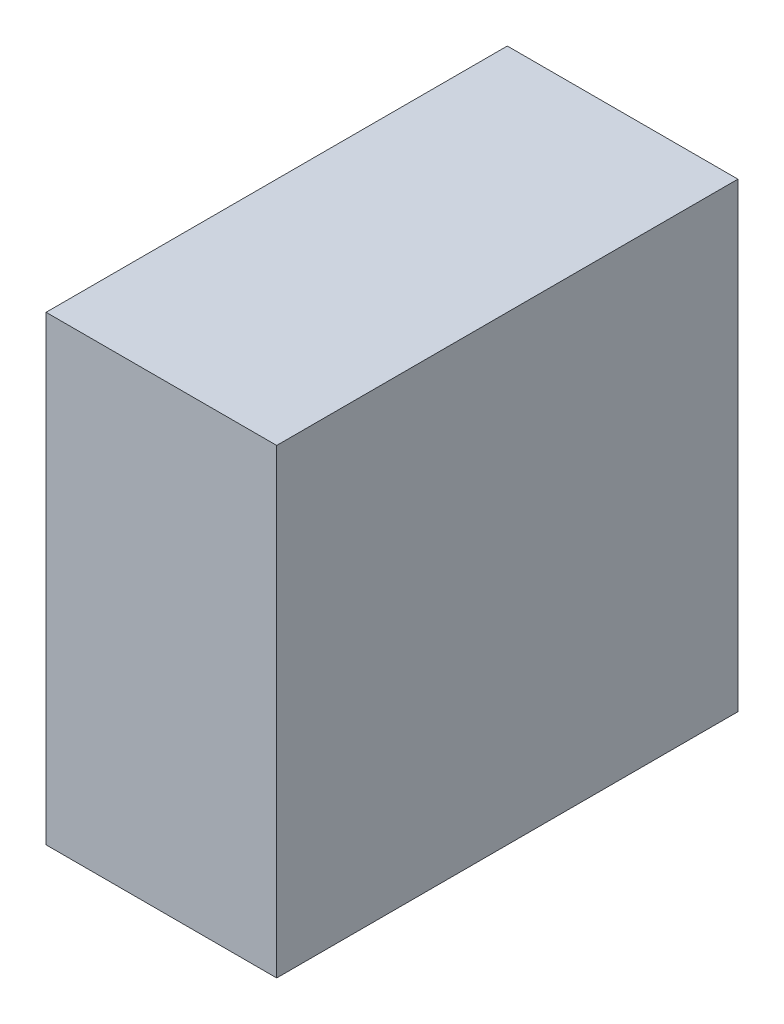
SolidWorks part; units mm, degrees
ref_plane "Front Plane" through (0, 0, 0) normal (0, 0, 1) x (1, 0, 0)
ref_plane "Top Plane" through (0, 0, 0) normal (0, 1, 0) x (1, 0, 0)
ref_plane "Right Plane" through (0, 0, 0) normal (1, 0, 0) x (0, 0, -1)
sketch "Sketch1" plane through (0, 0, 0) normal (0, 1, 0) x (1, 0, 0)
  line L1 (-15, -30) -> (15, -30)
  line L2 (-15, -30) -> (-15, 30)
  line L3 (-15, 30) -> (15, 30)
  line L4 (15, -30) -> (15, 30)
  line L5 (-15, -30) -> (15, 30) construction
  line L6 (-15, 30) -> (15, -30) construction
  point P0 (0, 0)
  dimension "D1" = 30
  dimension "D2" = 60
extrude "Boss-Extrude1" add sketch "Sketch1" along normal blind 60
